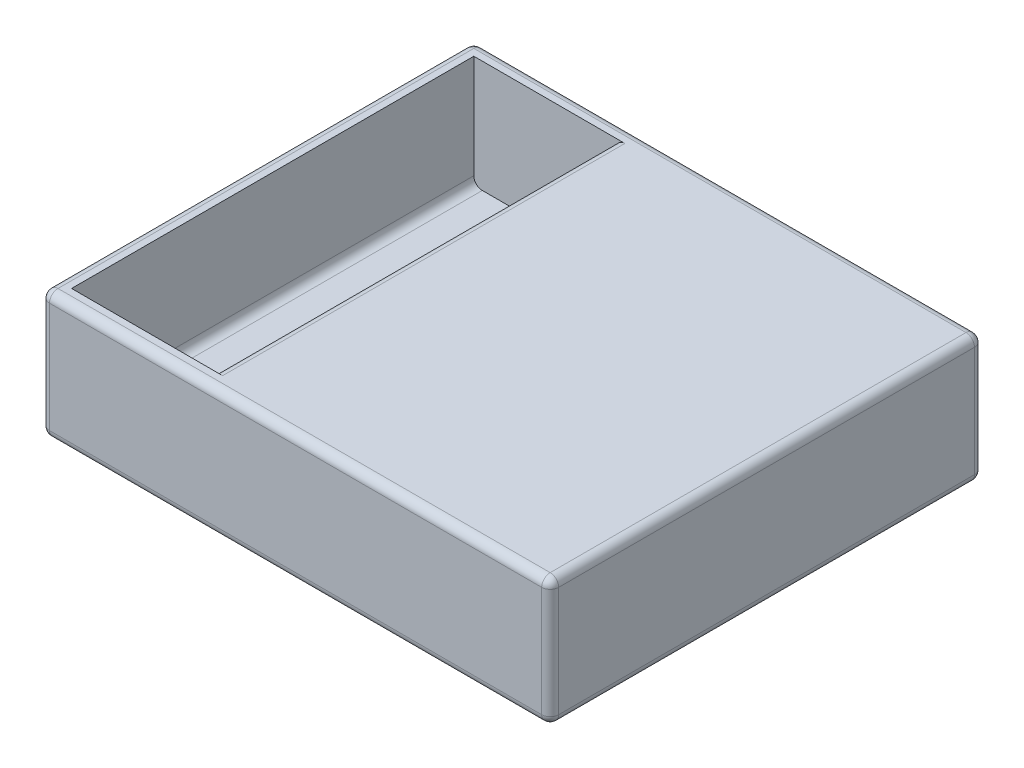
SolidWorks part; units mm, degrees
ref_plane "Front Plane" through (0, 0, 0) normal (0, 0, 1) x (1, 0, 0)
ref_plane "Top Plane" through (0, 0, 0) normal (0, 1, 0) x (1, 0, 0)
ref_plane "Right Plane" through (0, 0, 0) normal (1, 0, 0) x (0, 0, -1)
sketch "Sketch1" plane through (0, 0, 0) normal (0, 1, 0) x (1, 0, 0)
  line L12 (-65, 37.5) -> (-65, 45)
  line L14 (-65, 37.5) -> (-65, -32.5)
  line L16 (35, -32.5) -> (35, 37.5)
  line L18 (-65, 45) -> (35, 45)
  line L19 (35, 45) -> (35, -40)
  line L20 (35, -40) -> (-65, -40)
  line L21 (-65, -40) -> (-65, -32.5)
  circle A12 centre (-25, 17.5) radius 2.5
  circle A13 centre (25, 17.5) radius 2.5
  circle A14 centre (25, -17.5) radius 2.5
  circle A15 centre (-25, -17.5) radius 2.5
  point P0 (0, 0)
extrude "Boss-Extrude1" add sketch "Sketch1" along normal blind 25 contours L21 L20 L19 L16 L18 L12 L14 A15 A14 A13 A12
sketch "Sketch5" plane through (0, 25, 0) normal (0, 1, 0) x (1, 0, 0)
  line L8 (-62, 42) -> (-62, -37)
  line L9 (-62, -37) -> (32, -37)
  line L10 (32, -37) -> (32, 42)
  line L11 (32, 42) -> (-62, 42)
  line L12 (-62, 42) -> (-62, -37)
  line L13 (-62, -37) -> (32, -37)
  line L14 (32, -37) -> (32, 42)
  line L15 (32, 42) -> (-62, 42)
  dimension "D1" = 3
extrude "Cut-Extrude2" cut sketch "Sketch5" against normal blind 22
sketch "Sketch7" plane through (32, 0, 0) normal (-1, 0, 0) x (0, 0, 1)
  line L0 (-45, 25) -> (-45, 23)
  line L1 (-45, 25) -> (-45, 0) construction
  line L2 (-45, 23) -> (40, 23)
  line L3 (40, 25) -> (40, 0) construction
  line L4 (40, 23) -> (40, 25)
  line L5 (40, 25) -> (-45, 25)
extrude "Boss-Extrude4" add sketch "Sketch7" along normal blind 66
sketch "Sketch8" plane through (0, 0, 0) normal (0, -1, 0) x (1, 0, 0)
  circle A0 centre (0, -35.4924) radius 6.7
extrude "Cut-Extrude3" cut sketch "Sketch8" against normal blind 11
fillet "Fillet1" radius 1.67 15 edges at (-15, 25, 40) (-15, 0, 40) (-15, 25, -45) (-15, 0, -45) (35, 0, -2.5) (35, 25, -2.5) (-65, 0, -2.5) (32, 3, -2.5) (35, 12.5, 40) (-65, 12.5, 40) (-65, 12.5, -45) (35, 12.5, -45) (-34, 25, -2.5) (-65, 25, -2.5) (-62, 3, -2.5)
sketch "Sketch9" plane through (0, 3, 0) normal (0, 1, 0) x (1, 0, 0)
  circle A0 centre (-48.33, 2.5) radius 1.5
  circle A1 centre (-48.33, 30.3) radius 1.2
  circle A2 centre (-48.33, -25.3) radius 1.2
extrude "Cut-Extrude4" cut sketch "Sketch9" against normal blind 10
